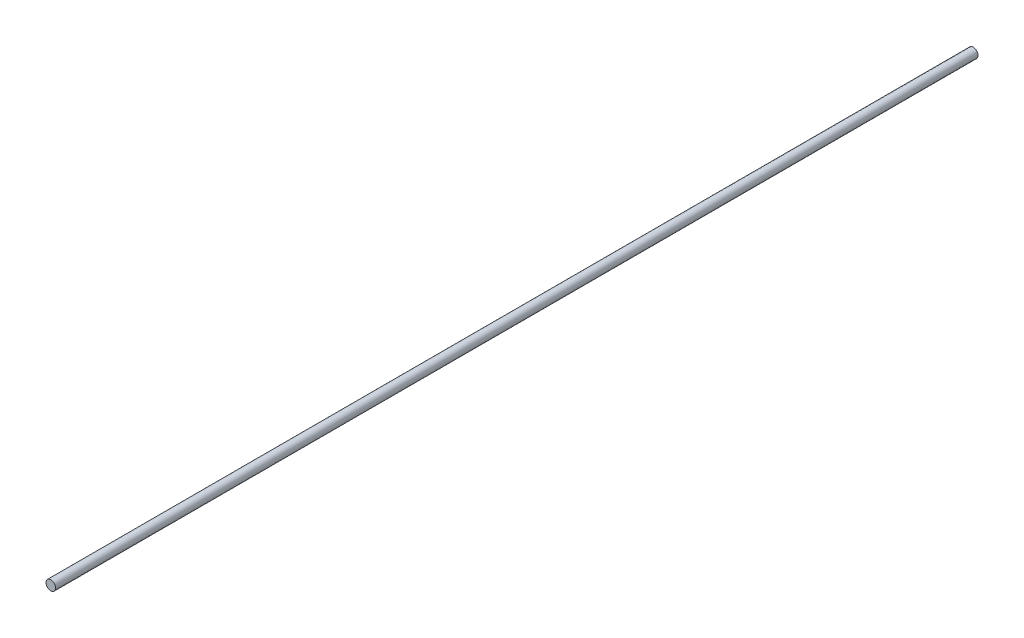
SolidWorks part; units mm, degrees
ref_plane "Front Plane" through (0, 0, 0) normal (0, 0, 1) x (1, 0, 0)
ref_plane "Top Plane" through (0, 0, 0) normal (0, 1, 0) x (1, 0, 0)
ref_plane "Right Plane" through (0, 0, 0) normal (1, 0, 0) x (0, 0, -1)
sketch "Sketch1" plane through (0, 0, 0) normal (0, 0, 1) x (1, 0, 0)
  circle A0 centre (0, 0) radius 10
  dimension "D1" = 20
extrude "Boss-Extrude1" add sketch "Sketch1" along normal blind 1920
